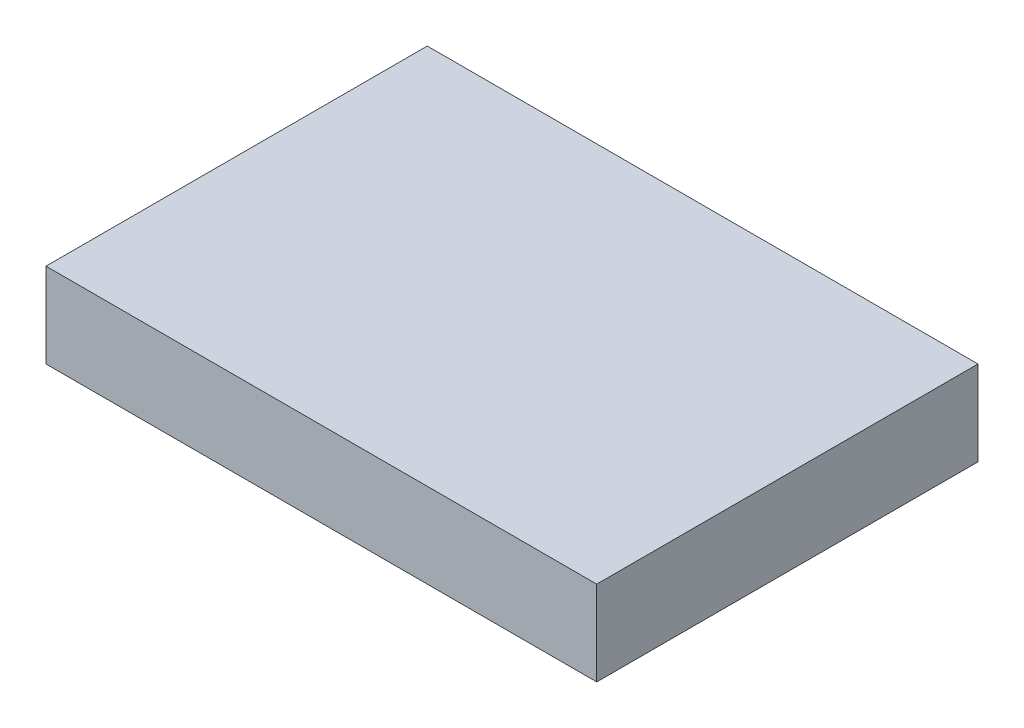
SolidWorks part; units mm, degrees
ref_plane "Front Plane" through (0, 0, 0) normal (0, 0, 1) x (1, 0, 0)
ref_plane "Top Plane" through (0, 0, 0) normal (0, 1, 0) x (1, 0, 0)
ref_plane "Right Plane" through (0, 0, 0) normal (1, 0, 0) x (0, 0, -1)
sketch "Sketch1" plane through (0, 0, 0) normal (0, 1, 0) x (1, 0, 0)
  line L1 (0, 0) -> (65, 0)
  line L2 (0, 0) -> (0, -45)
  line L3 (0, -45) -> (65, -45)
  line L4 (65, 0) -> (65, -45)
  dimension "D1" = 65
  dimension "D2" = 45
extrude "Boss-Extrude1" add sketch "Sketch1" along normal blind 10
